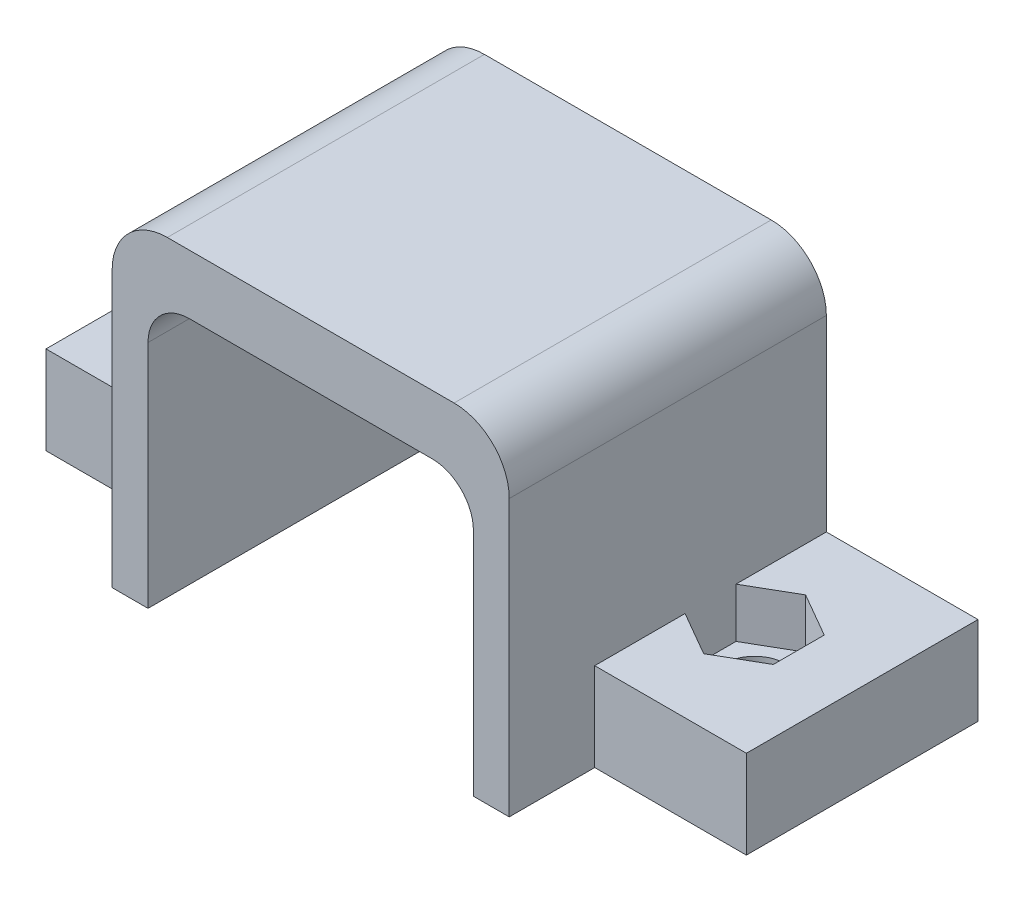
SolidWorks part; units mm, degrees
material "尼龙 101"
ref_plane "前视基准面" through (0, 0, 0) normal (0, 0, 1) x (1, 0, 0)
ref_plane "上视基准面" through (0, 0, 0) normal (0, 1, 0) x (1, 0, 0)
ref_plane "右视基准面" through (0, 0, 0) normal (1, 0, 0) x (0, 0, -1)
other "Configuration Table"
sketch "草图1" plane through (0, 0, 0) normal (0, 0, 1) x (1, 0, 0)
  line L0 (13.1, 0) -> (14.4, 0)
  line L5 (0, 0) -> (1.3, 0)
  line L6 (0, 0) -> (0, 12)
  line L7 (0, 12) -> (14.4, 12)
  line L8 (14.4, 0) -> (14.4, 12)
  line L10 (1.3, 0) -> (1.3, 9.85)
  line L11 (1.3, 9.85) -> (13.1, 9.85)
  line L12 (13.1, 0) -> (13.1, 9.85)
  dimension "D1" = 14.4
  dimension "D2" = 12
  dimension "D3" = 1.3
  dimension "D4" = 1.3
  dimension "D5" = 9.85
extrude "凸台-拉伸1" add sketch "草图1" along normal blind 11.5
sketch "草图2" plane through (0, 0, 0) normal (0, -1, 0) x (1, 0, 0)
  line L1 (0, 0) -> (-5.5, 0)
  line L2 (0, 0) -> (0, 8.4)
  line L3 (0, 8.4) -> (-5.5, 8.4)
  line L4 (-5.5, 0) -> (-5.5, 8.4)
  line L5 (14.4, 0) -> (19.9, 0)
  line L6 (14.4, 0) -> (14.4, 8.4)
  line L7 (14.4, 8.4) -> (19.9, 8.4)
  line L8 (19.9, 0) -> (19.9, 8.4)
  dimension "D1" = 8.4
  dimension "D2" = 25.4
extrude "凸台-拉伸2" add sketch "草图2" against normal blind 3.2
sketch "草图3" plane through (0, 3.2, 0) normal (0, 1, 0) x (1, 0, 0)
  line L0 (-5.5, -4.2) -> (19.9, -4.2) construction
  line L1 (-5.5, -8.4) -> (-5.5, 0) construction
  line L2 (19.9, 0) -> (19.9, -8.4) construction
  circle A0 centre (-1.6, -4.2) radius 1.125
  circle A1 centre (16, -4.2) radius 1.125
  point P12 (7.0458, -4.2)
  dimension "D1" = 2.25
  dimension "D2" = 2.25
  dimension "D3" = 17.6
  dimension "D4" = 3.9
extrude "切除-拉伸1" cut sketch "草图3" against normal through all
sketch "草图4" plane through (0, 3.2, 0) normal (0, 1, 0) x (1, 0, 0)
  line L0 (-1.6, -4.2) -> (16, -4.2) construction
  line L1 (14.4, -11.5) -> (14.4, 0) construction
  line L2 (-1.6, -2.3525) -> (-3.2, -3.2762)
  line L3 (-3.2, -3.2762) -> (-3.2, -5.1238)
  line L4 (-3.2, -5.1238) -> (-1.6, -6.0475)
  line L5 (-1.6, -6.0475) -> (0, -5.1238)
  line L6 (0, -5.1238) -> (0, -3.2762)
  line L7 (0, -3.2762) -> (-1.6, -2.3525)
  line L8 (16, -2.3525) -> (14.4, -3.2762)
  line L9 (14.4, -3.2762) -> (14.4, -5.1238)
  line L10 (14.4, -5.1238) -> (16, -6.0475)
  line L11 (16, -6.0475) -> (17.6, -5.1238)
  line L12 (17.6, -5.1238) -> (17.6, -3.2762)
  line L13 (17.6, -3.2762) -> (16, -2.3525)
  line L14 (0, -11.5) -> (0, 0) construction
  circle A0 centre (-1.6, -4.2) radius 1.6 construction
  circle A1 centre (16, -4.2) radius 1.6 construction
extrude "切除-拉伸2" cut sketch "草图4" against normal blind 1.8
fillet "圆角2" radius 2 2 edges at (0, 12, 5.75) (14.4, 12, 5.75)
fillet "圆角3" radius 1.5 2 edges at (13.1, 9.85, 5.75) (1.3, 9.85, 5.75)
